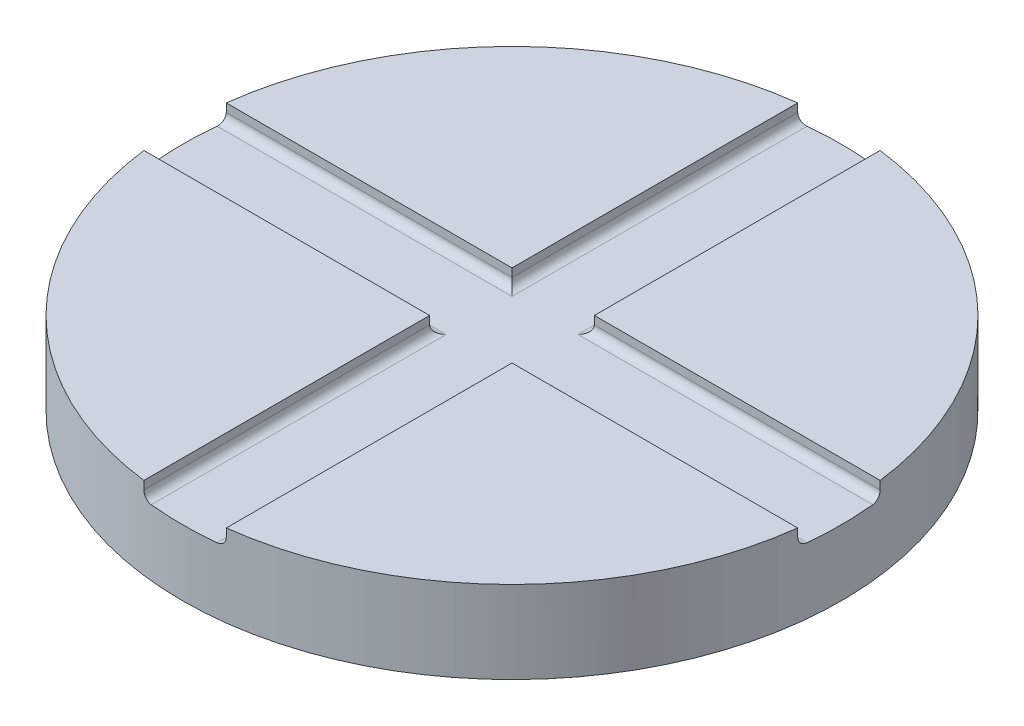
SolidWorks part; units mm, degrees
material "Flywheel"
ref_plane "Front Plane" through (0, 0, 0) normal (0, 0, 1) x (1, 0, 0)
ref_plane "Top Plane" through (0, 0, 0) normal (0, 1, 0) x (1, 0, 0)
ref_plane "Right Plane" through (0, 0, 0) normal (1, 0, 0) x (0, 0, -1)
sketch "Sketch1" plane through (0, 0, 0) normal (0, 1, 0) x (1, 0, 0)
  circle A0 centre (0, 0) radius 40
extrude "Boss-Extrude1" add sketch "Sketch1" along normal blind 10
sketch "Sketch7" plane through (0, 10, 0) normal (0, 1, 0) x (1, 0, 0)
  line L0 (-5, 39.6863) -> (-5, 5)
  line L1 (5, -39.6863) -> (5, -5)
  line L2 (39.6863, -5) -> (5, -5)
  line L3 (39.6863, 5) -> (5, 5)
  line L4 (-5, -5) -> (-39.6863, -5)
  line L5 (0, -5.5) -> (0, 5.5) construction
  line L6 (-83.1027, 0) -> (-40, 0) construction
  line L7 (40, 0) -> (59.2378, 0) construction
  line L8 (-5, 5) -> (-39.6863, 5)
  line L9 (5, 5) -> (5, 39.6863)
  line L10 (-5, -5) -> (-5, -39.6863)
  circle A0 centre (0, 0) radius 40 construction
  arc A1 (5, 39.6863) -> (-5, 39.6863) centre (0, 0) ccw
  arc A2 (39.6863, -5) -> (39.6863, 5) centre (0, 0) ccw
  arc A3 (-5, -39.6863) -> (5, -39.6863) centre (0, 0) ccw
  arc A4 (-39.6863, -5) -> (-39.6863, 5) centre (0, 0) cw
  dimension "D1" = 5
  dimension "D2" = 5
  dimension "D3" = 5
  dimension "D4" = 5
  dimension "D5" = 10
  dimension "D6" = 10
  dimension "D7" = 10
  dimension "D8" = 10
  dimension "D9" = 90
  dimension "D10" = 5
  dimension "D11" = 90
extrude "Cut-Extrude2" cut sketch "Sketch7" against normal blind 2
fillet "Fillet1" radius 1 8 edges at (22.3431, 8, -5) (22.3431, 8, 5) (5, 8, 22.3431) (5, 8, -22.3431) (-5, 8, -22.3431) (-22.3431, 8, -5) (-22.3431, 8, 5) (-5, 8, 22.3431)
